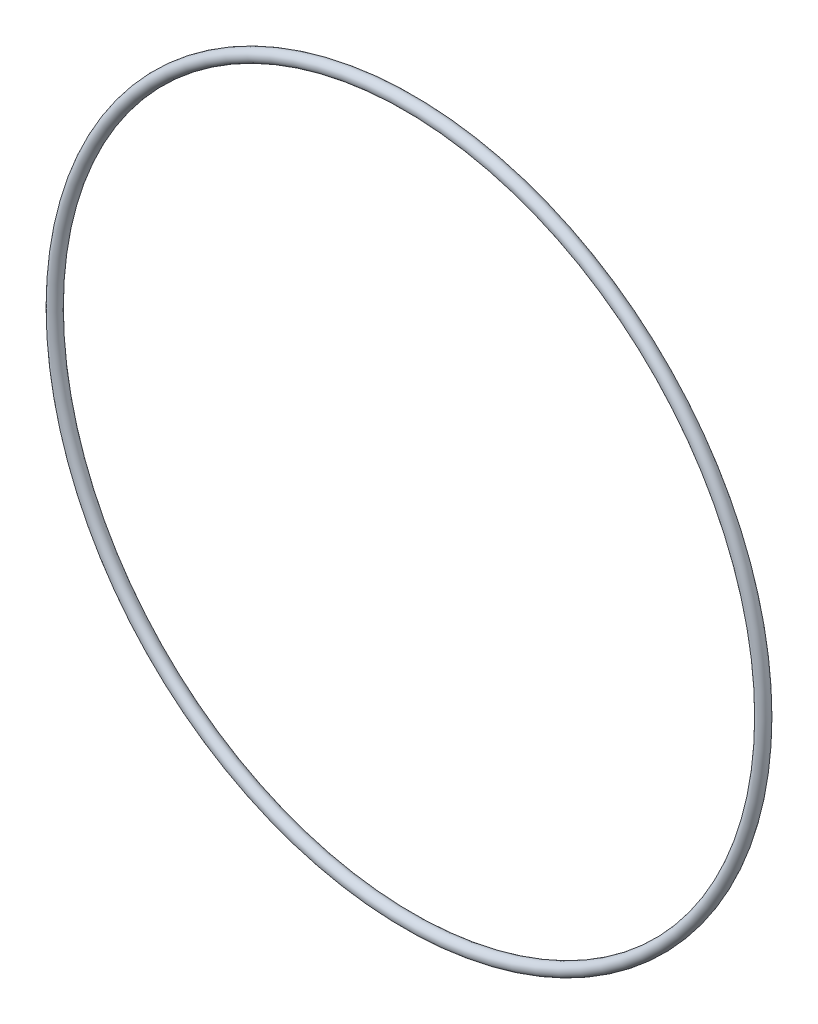
SolidWorks part; units mm, degrees
ref_plane "Front" through (0, 0, 0) normal (0, 0, 1) x (1, 0, 0)
ref_plane "Top" through (0, 0, 0) normal (0, 1, 0) x (1, 0, 0)
ref_plane "Right" through (0, 0, 0) normal (1, 0, 0) x (0, 0, -1)
sketch "Sketch1" plane through (0, 0, 0) normal (1, 0, 0) x (0, -1, 0)
  line L0 (0, -0.889) -> (0, 0.889) construction
  line L2 (-57.6821, 0) -> (57.6821, 0) construction
  line L3 (-50.6603, 0) -> (50.6603, 0) construction
  circle A0 centre (51.5493, 0) radius 0.889
  point P9 (50.6603, 0)
  point P10 (52.4383, 0)
  point P13 (51.5493, 0.889)
  point P14 (51.5493, -0.889)
  dimension "Width" = 1.778
  dimension "ID" = 101.3206
revolve "Revolve1" add sketch "Sketch1" angle 360 about L0
